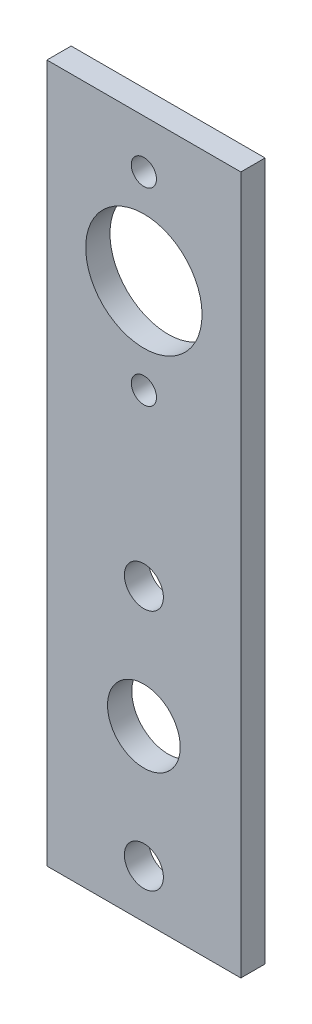
SolidWorks part; units mm, degrees
ref_plane "Front Plane" through (0, 0, 0) normal (0, 0, 1) x (1, 0, 0)
ref_plane "Top Plane" through (0, 0, 0) normal (0, 1, 0) x (1, 0, 0)
ref_plane "Right Plane" through (0, 0, 0) normal (1, 0, 0) x (0, 0, -1)
sketch "Sketch1" plane through (0, 0, 0) normal (0, 0, 1) x (1, 0, 0)
  line L1 (0, 0) -> (25.4, 0)
  line L2 (0, 0) -> (0, 91.44)
  line L3 (0, 91.44) -> (25.4, 91.44)
  line L4 (25.4, 0) -> (25.4, 91.44)
  dimension "D1" = 25.4
  dimension "D2" = 91.44
extrude "Boss-Extrude1" add sketch "Sketch1" along normal blind 3.175
sketch "Sketch2" plane through (0, 0, 3.175) normal (0, 0, 1) x (1, 0, 0)
  line L0 (0, 0) -> (25.4, 0) construction
  line L2 (12.7, 38.1) -> (12.7, 6.35) construction
  circle A0 centre (12.7, 6.35) radius 2.5527
  circle A1 centre (12.7, 38.1) radius 2.5527
  circle A2 centre (12.7, 22.225) radius 4.7625
  point P6 (12.7, 0)
  dimension "D1" = 5.1054
  dimension "D2" = 31.75
  dimension "D4" = 9.525
  dimension "D3" = 6.35
extrude "Cut-Extrude1" cut sketch "Sketch2" against normal blind 3.175
sketch "Sketch3" plane through (0, 0, 3.175) normal (0, 0, 1) x (1, 0, 0)
  line L0 (25.4, 91.44) -> (0, 91.44) construction
  line L1 (12.7, 85.09) -> (12.7, 60.325) construction
  circle A0 centre (12.7, 85.09) radius 1.651
  circle A1 centre (12.7, 60.325) radius 1.651
  circle A2 centre (12.7, 72.7075) radius 7.62
  point P8 (12.7, 91.44)
  dimension "D1" = 3.302
  dimension "D4" = 15.24
  dimension "D2" = 24.765
  dimension "D3" = 6.35
extrude "Cut-Extrude2" cut sketch "Sketch3" against normal blind 3.175 contours A0 | A1 | A2
